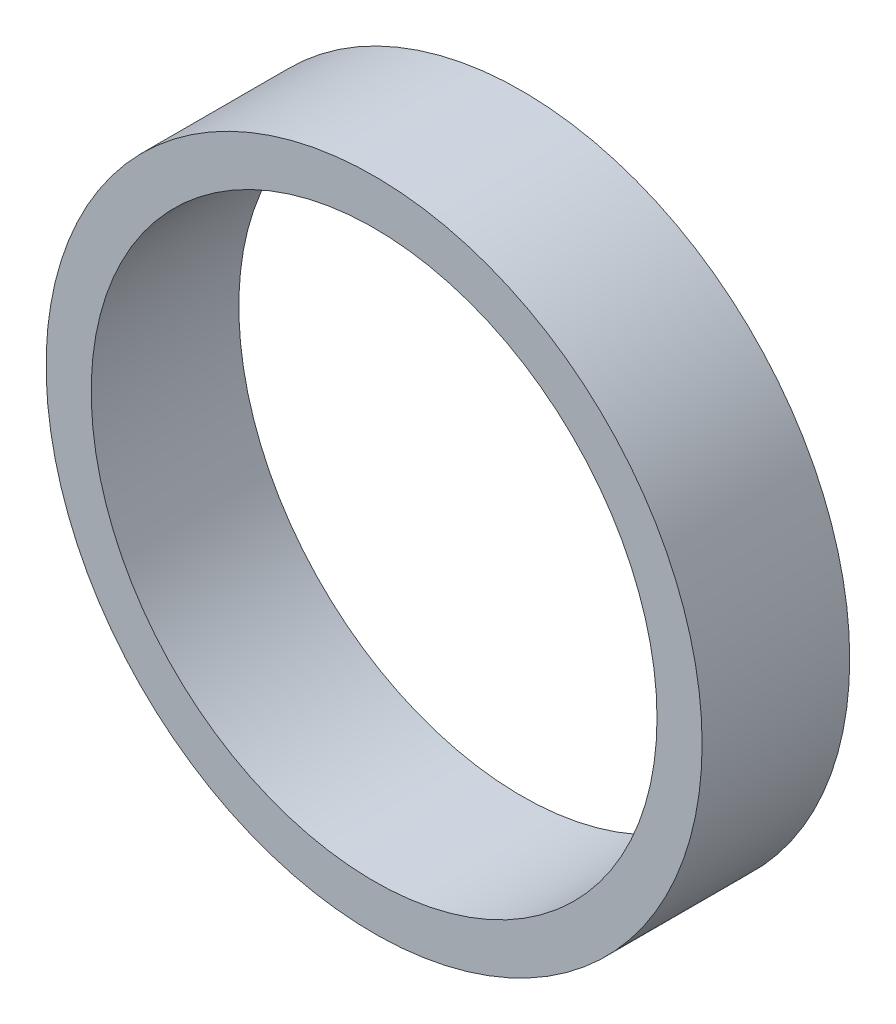
SolidWorks part; units mm, degrees
ref_plane "Front Plane" through (0, 0, 0) normal (0, 0, 1) x (1, 0, 0)
ref_plane "Top Plane" through (0, 0, 0) normal (0, 1, 0) x (1, 0, 0)
ref_plane "Right Plane" through (0, 0, 0) normal (1, 0, 0) x (0, 0, -1)
sketch "Sketch1" plane through (0, 0, 0) normal (0, 0, 1) x (1, 0, 0)
  circle A0 centre (0, 0) radius 20
extrude "Boss-Extrude1" add sketch "Sketch1" along normal mid plane 9
sketch "Sketch2" plane through (0, 0, 4.5) normal (0, 0, 1) x (1, 0, 0)
  circle A0 centre (0, 0) radius 17.25
extrude "Cut-Extrude1" cut sketch "Sketch2" against normal blind 9
